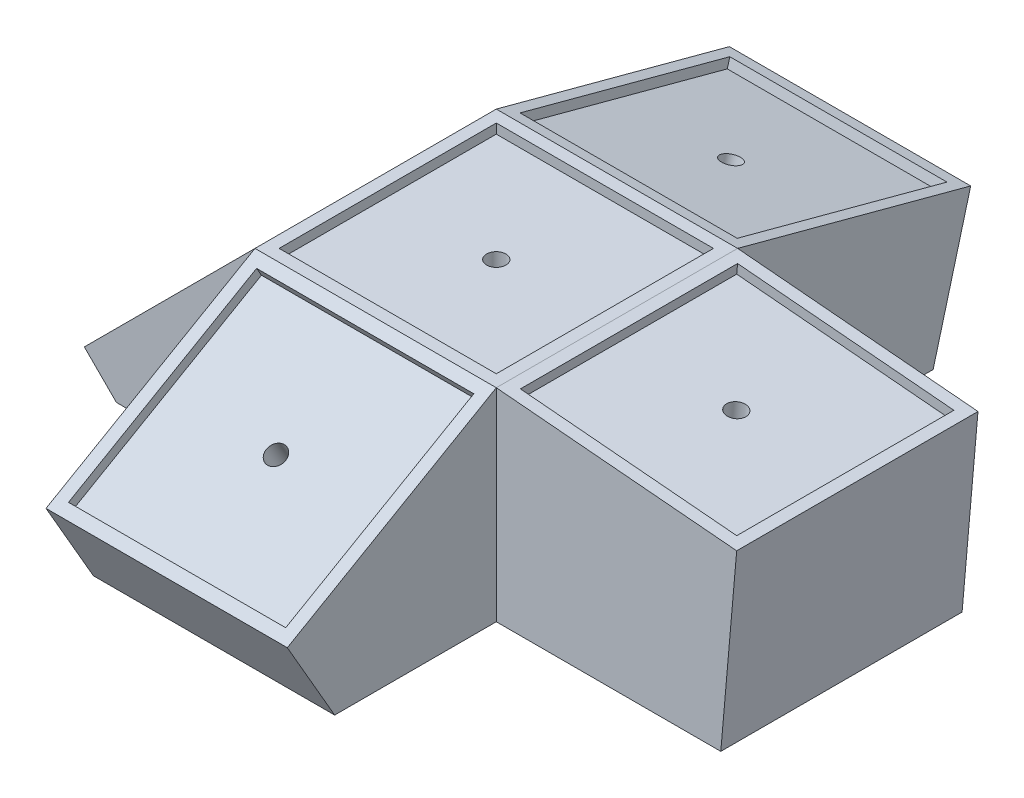
SolidWorks part; units mm, degrees
ref_plane "Front Plane" through (0, 0, 0) normal (0, 0, 1) x (1, 0, 0)
ref_plane "Top Plane" through (0, 0, 0) normal (0, 1, 0) x (1, 0, 0)
ref_plane "Right Plane" through (0, 0, 0) normal (1, 0, 0) x (0, 0, -1)
sketch "Sketch1" plane through (0, 0, 0) normal (0, 1, 0) x (1, 0, 0)
  line L1 (0, 0) -> (57.15, 0)
  line L2 (0, 0) -> (0, 57.15)
  line L3 (0, 57.15) -> (57.15, 57.15)
  line L4 (57.15, 0) -> (57.15, 57.15)
  line L5 (-3.175, 60.325) -> (60.325, 60.325)
  line L6 (-3.175, 60.325) -> (-3.175, -3.175)
  line L7 (-3.175, -3.175) -> (60.325, -3.175)
  line L8 (60.325, 60.325) -> (60.325, -3.175)
  dimension "D1" = 57.15
  dimension "D2" = 57.15
  dimension "D3" = 3.175
  dimension "D4" = 3.175
  dimension "D5" = 3.175
  dimension "D6" = 3.175
extrude "Boss-Extrude1" add sketch "Sketch1" along normal blind 2.54
sketch "Sketch2" plane through (0, 0, 0) normal (0, -1, 0) x (1, 0, 0)
  line L1 (-3.175, 3.175) -> (60.325, 3.175)
  line L2 (-3.175, 3.175) -> (-3.175, -60.325)
  line L3 (-3.175, -60.325) -> (60.325, -60.325)
  line L4 (60.325, 3.175) -> (60.325, -60.325)
extrude "Boss-Extrude2" add sketch "Sketch2" along normal blind 8.89
sketch "Sketch3" plane through (0, 0, 0) normal (0, 1, 0) x (1, 0, 0)
  line L1 (-3.175, -3.175) -> (60.325, -3.175) construction
  line L2 (60.325, -3.175) -> (60.325, 60.325) construction
  circle A0 centre (28.575, 28.575) radius 2.54
  dimension "D1" = 5.08
  dimension "D2" = 31.75
  dimension "D3" = 31.75
extrude "Cut-Extrude1" cut sketch "Sketch3" against normal blind 8.89
ref_plane "Plane1" through (0.6788, 7.7584, 0) normal (0.0872, 0.9962, 0) x (0, 0, -1)
sketch "Sketch4" plane through (0.6788, 7.7584, 0) normal (0.0872, 0.9962, 0) x (0, 0, -1)
  line L1 (-3.175, -59.8741) -> (60.325, -59.8741)
  line L2 (-3.175, -59.8741) -> (-3.175, -123.3741)
  line L3 (-3.175, -123.3741) -> (60.325, -123.3741)
  line L4 (60.325, -59.8741) -> (60.325, -123.3741)
  line L6 (0, -63.0491) -> (57.15, -63.0491)
  line L7 (0, -63.0491) -> (0, -120.1991)
  line L8 (0, -120.1991) -> (57.15, -120.1991)
  line L9 (57.15, -63.0491) -> (57.15, -120.1991)
  line L12 (-3.175, -59.8741) -> (60.325, -59.8741) construction
  line L13 (60.325, -59.8741) -> (60.325, 3.3843) construction
  dimension "D1" = 63.5
  dimension "D2" = 63.5
  dimension "D3" = 57.15
  dimension "D4" = 57.15
  dimension "D5" = 3.175
  dimension "D6" = 3.175
extrude "Boss-Extrude3" add sketch "Sketch4" against normal blind 2.54 separate body
sketch "Sketch5" plane through (0.4574, 5.228, 0) normal (-0.0872, -0.9962, 0) x (0.9962, -0.0872, 0)
  line L0 (59.8741, 3.175) -> (123.3741, 3.175) construction
  line L1 (59.8741, 3.175) -> (123.3741, 3.175)
  line L2 (59.8741, 3.175) -> (59.8741, -60.325)
  line L3 (59.8741, -60.325) -> (123.3741, -60.325)
  line L4 (123.3741, 3.175) -> (123.3741, -60.325)
  dimension "D1" = 63.5
extrude "Boss-Extrude4" add sketch "Sketch5" along normal blind 8.89
sketch "Sketch6" plane through (0.4574, 5.228, 0) normal (0.0872, 0.9962, 0) x (0.9962, -0.0872, 0)
  line L0 (123.3741, -3.175) -> (123.3741, 60.325) construction
  line L1 (59.8741, -3.175) -> (123.3741, -3.175) construction
  circle A0 centre (91.6241, 28.575) radius 2.54
  dimension "D1" = 31.75
  dimension "D3" = 5.08
  dimension "D2" = 31.75
extrude "Cut-Extrude2" cut sketch "Sketch6" against normal blind 8.89
ref_plane "Plane2" through (0, 17.4511, -4.676) normal (0, 0.9659, -0.2588) x (-1, 0, 0)
sketch "Sketch7" plane through (0, 17.4511, -4.676) normal (0, 0.9659, -0.2588) x (-1, 0, 0)
  line L1 (-60.325, -57.6121) -> (3.175, -57.6121)
  line L2 (-60.325, -57.6121) -> (-60.325, -121.1121)
  line L3 (-60.325, -121.1121) -> (3.175, -121.1121)
  line L4 (3.175, -57.6121) -> (3.175, -121.1121)
  line L5 (-57.15, -60.7871) -> (0, -60.7871)
  line L6 (-57.15, -60.7871) -> (-57.15, -117.9371)
  line L7 (-57.15, -117.9371) -> (0, -117.9371)
  line L8 (0, -60.7871) -> (0, -117.9371)
  dimension "D1" = 63.5
  dimension "D2" = 63.5
  dimension "D3" = 57.15
  dimension "D4" = 57.15
  dimension "D5" = 3.175
  dimension "D6" = 3.175
extrude "Boss-Extrude5" add sketch "Sketch7" against normal blind 2.54
sketch "Sketch8" plane through (0, 14.9977, -4.0186) normal (0, -0.9659, 0.2588) x (1, 0, 0)
  line L0 (60.325, -58.2927) -> (60.325, -121.1121) construction
  line L1 (-3.175, -121.1121) -> (60.325, -121.1121)
  line L2 (-3.175, -121.1121) -> (-3.175, -57.6121)
  line L3 (-3.175, -57.6121) -> (60.325, -57.6121)
  line L4 (60.325, -121.1121) -> (60.325, -57.6121)
  dimension "D1" = 63.5
extrude "Boss-Extrude6" add sketch "Sketch8" along normal blind 8.89
sketch "Sketch9" plane through (0, 14.9977, -4.0186) normal (0, 0.9659, -0.2588) x (1, 0, 0)
  line L0 (60.325, 57.6121) -> (-3.175, 57.6121) construction
  line L1 (-3.175, 121.1121) -> (-3.175, 57.6121) construction
  circle A0 centre (28.575, 89.3621) radius 2.54
  point P6 (0, 0)
  dimension "D1" = 31.75
  dimension "D3" = 5.08
  dimension "D2" = 31.75
extrude "Cut-Extrude3" cut sketch "Sketch9" against normal blind 8.89
ref_plane "Plane3" through (0, 3.2798, 1.8936) normal (0, 0.866, 0.5) x (1, 0, 0)
sketch "Sketch10" plane through (0, 3.2798, 1.8936) normal (0, 0.866, 0.5) x (1, 0, 0)
  line L1 (-3.175, -1.4796) -> (60.325, -1.4796)
  line L2 (-3.175, -1.4796) -> (-3.175, -64.9796)
  line L3 (-3.175, -64.9796) -> (60.325, -64.9796)
  line L4 (60.325, -1.4796) -> (60.325, -64.9796)
  line L5 (0, -4.6546) -> (57.15, -4.6546)
  line L6 (0, -4.6546) -> (0, -61.8046)
  line L7 (0, -61.8046) -> (57.15, -61.8046)
  line L8 (57.15, -4.6546) -> (57.15, -61.8046)
  dimension "D1" = 63.5
  dimension "D2" = 63.5
  dimension "D3" = 57.15
  dimension "D4" = 57.15
  dimension "D5" = 3.175
  dimension "D6" = 3.175
extrude "Boss-Extrude7" add sketch "Sketch10" against normal blind 2.54
sketch "Sketch11" plane through (0, 1.0801, 0.6236) normal (0, -0.866, -0.5) x (1, 0, 0)
  line L0 (60.325, 64.9796) -> (60.325, 2.9461) construction
  line L1 (-3.175, 64.9796) -> (60.325, 64.9796)
  line L2 (-3.175, 64.9796) -> (-3.175, 1.4796)
  line L3 (-3.175, 1.4796) -> (60.325, 1.4796)
  line L4 (60.325, 64.9796) -> (60.325, 1.4796)
  dimension "D1" = 63.5
extrude "Boss-Extrude8" add sketch "Sketch11" along normal blind 8.89
sketch "Sketch12" plane through (0, 1.0801, 0.6236) normal (0, 0.866, 0.5) x (1, 0, 0)
  line L0 (-3.175, -1.4796) -> (60.325, -1.4796) construction
  line L1 (-3.175, -1.4796) -> (-3.175, -64.9796) construction
  circle A0 centre (28.575, -33.2296) radius 2.54
  dimension "D1" = 31.75
  dimension "D3" = 5.08
  dimension "D2" = 31.75
extrude "Cut-Extrude4" cut sketch "Sketch12" against normal blind 8.89
ref_plane "Plane4" through (-2.8575, 2.8575, 0) normal (-0.7071, 0.7071, 0) x (0, 0, 1)
sketch "Sketch14" plane through (-2.8575, 2.8575, 0) normal (-0.7071, 0.7071, 0) x (0, 0, 1)
  line L1 (-60.325, -0.449) -> (3.175, -0.449)
  line L2 (-60.325, -0.449) -> (-60.325, -63.949)
  line L3 (-60.325, -63.949) -> (3.175, -63.949)
  line L4 (3.175, -0.449) -> (3.175, -63.949)
  line L5 (-57.15, -3.624) -> (0, -3.624)
  line L6 (-57.15, -3.624) -> (-57.15, -60.774)
  line L7 (-57.15, -60.774) -> (0, -60.774)
  line L8 (0, -3.624) -> (0, -60.774)
  dimension "D1" = 63.5
  dimension "D2" = 63.5
  dimension "D3" = 57.15
  dimension "D4" = 57.15
  dimension "D5" = 3.175
  dimension "D6" = 3.175
extrude "Boss-Extrude10" add sketch "Sketch14" against normal blind 2.54
sketch "Sketch15" plane through (-1.0614, 1.0614, 0) normal (0.7071, -0.7071, 0) x (0, 0, -1)
  line L0 (60.325, -2.989) -> (60.325, -63.949) construction
  line L1 (-3.175, -63.949) -> (60.325, -63.949)
  line L2 (-3.175, -63.949) -> (-3.175, -0.449)
  line L3 (-3.175, -0.449) -> (60.325, -0.449)
  line L4 (60.325, -63.949) -> (60.325, -0.449)
  dimension "D1" = 63.5
extrude "Boss-Extrude11" add sketch "Sketch15" along normal blind 8.89
sketch "Sketch16" plane through (-1.0614, 1.0614, 0) normal (-0.7071, 0.7071, 0) x (0, 0, 1)
  line L0 (-60.325, -63.949) -> (3.175, -63.949) construction
  line L1 (-60.325, -0.449) -> (-60.325, -63.949) construction
  circle A0 centre (-28.575, -32.199) radius 2.54
  dimension "D1" = 31.75
  dimension "D3" = 5.08
  dimension "D2" = 31.75
extrude "Cut-Extrude5" cut sketch "Sketch16" against normal blind 8.89
ref_plane "Plane5" through (0, -50.8, 0) normal (0, 1, 0) x (1, 0, 0)
sketch "Sketch18" plane through (0, -50.8, 0) normal (0, 1, 0) x (1, 0, 0)
  line L1 (60.325, 60.325) -> (123.5834, 60.325)
  line L2 (60.325, 60.325) -> (60.325, -3.175)
  line L3 (60.325, -3.175) -> (123.5834, -3.175)
  line L4 (123.5834, 60.325) -> (123.5834, -3.175)
extrude "Boss-Extrude12" add sketch "Sketch18" along normal up to surface (36.3319 mm away)
sketch "Sketch19" plane through (-0.3174, -3.6281, 0) normal (0.0872, 0.9962, 0) x (0.9962, -0.0872, 0)
  line L1 (123.3741, 60.325) -> (144.6746, 60.325)
  line L2 (123.3741, 60.325) -> (123.3741, -3.175)
  line L3 (123.3741, -3.175) -> (144.6746, -3.175)
  line L4 (144.6746, 60.325) -> (144.6746, -3.175)
extrude "Cut-Extrude7" cut sketch "Sketch19" against normal up to surface (34.6947 mm away)
sketch "Sketch20" plane through (0, -50.8, 0) normal (0, 1, 0) x (1, 0, 0)
  line L0 (0, 0) -> (57.15, 0) construction
  line L1 (-3.175, 0) -> (60.325, 0)
  line L2 (-3.175, 0) -> (-3.175, -58.1676)
  line L3 (-3.175, -58.1676) -> (60.325, -58.1676)
  line L4 (60.325, 0) -> (60.325, -58.1676)
  line L5 (-3.175, -3.175) -> (-3.175, -58.1676) construction
extrude "Boss-Extrude15" add sketch "Sketch20" along normal up to surface (41.9749 mm away)
sketch "Sketch21" plane through (0, -6.6189, -3.8214) normal (0, 0.866, 0.5) x (1, 0, 0)
  line L0 (60.325, -64.9796) -> (60.325, -71.5787) construction
  line L1 (-3.175, -64.9796) -> (60.325, -64.9796)
  line L2 (-3.175, -64.9796) -> (-3.175, -101.2856)
  line L3 (-3.175, -101.2856) -> (60.325, -101.2856)
  line L4 (60.325, -64.9796) -> (60.325, -101.2856)
extrude "Cut-Extrude8" cut sketch "Sketch21" against normal up to surface (13.5 mm away)
sketch "Sketch22" plane through (0, -50.8, 0) normal (0, 1, 0) x (1, 0, 0)
  line L0 (-3.175, -3.175) -> (60.325, -3.175) construction
  line L1 (-48.0763, 60.325) -> (0, 60.325)
  line L2 (-48.0763, 60.325) -> (-48.0763, -3.175)
  line L3 (-48.0763, -3.175) -> (0, -3.175)
  line L4 (0, 60.325) -> (0, -3.175)
extrude "Boss-Extrude16" add sketch "Sketch22" along normal up to surface (40.3505 mm away)
sketch "Sketch23" plane through (5.2247, -5.2247, 0) normal (-0.7071, 0.7071, 0) x (0, 0, 1)
  line L0 (3.175, -64.4532) -> (3.175, -63.949) construction
  line L1 (-60.325, -63.949) -> (3.175, -63.949)
  line L2 (-60.325, -63.949) -> (-60.325, -68.8645)
  line L3 (-60.325, -68.8645) -> (3.175, -68.8645)
  line L4 (3.175, -63.949) -> (3.175, -68.8645)
extrude "Cut-Extrude9" cut sketch "Sketch23" against normal up to surface (0.5042 mm away)
sketch "Sketch24" plane through (0, -50.8, 0) normal (0, 1, 0) x (1, 0, 0)
  line L0 (57.15, 57.15) -> (0, 57.15) construction
  line L1 (-3.175, 121.6613) -> (60.325, 121.6613)
  line L2 (-3.175, 121.6613) -> (-3.175, 57.15)
  line L3 (-3.175, 57.15) -> (60.325, 57.15)
  line L4 (60.325, 121.6613) -> (60.325, 57.15)
  line L5 (60.325, 60.325) -> (60.325, 121.6613) construction
extrude "Boss-Extrude18" add sketch "Sketch24" along normal up to surface (25.0718 mm away)
sketch "Sketch25" plane through (0, 6.4106, -1.7177) normal (0, 0.9659, -0.2588) x (1, 0, 0)
  line L0 (-3.175, 124.1747) -> (-3.175, 121.1121) construction
  line L1 (-3.175, 144.5559) -> (60.325, 144.5559)
  line L2 (-3.175, 144.5559) -> (-3.175, 121.1121)
  line L3 (-3.175, 121.1121) -> (60.325, 121.1121)
  line L4 (60.325, 144.5559) -> (60.325, 121.1121)
extrude "Cut-Extrude10" cut sketch "Sketch25" against normal up to surface (20.4951 mm away)
sketch "Sketch26" plane through (0, -50.8, 0) normal (0, 1, 0) x (1, 0, 0)
  line L1 (-3.175, 60.325) -> (60.325, 60.325)
  line L2 (-3.175, 60.325) -> (-3.175, -3.175)
  line L3 (-3.175, -3.175) -> (60.325, -3.175)
  line L4 (60.325, 60.325) -> (60.325, -3.175)
extrude "Boss-Extrude19" add sketch "Sketch26" along normal up to surface (41.91 mm away) up to face at (28.575, -8.89, -26.035)
